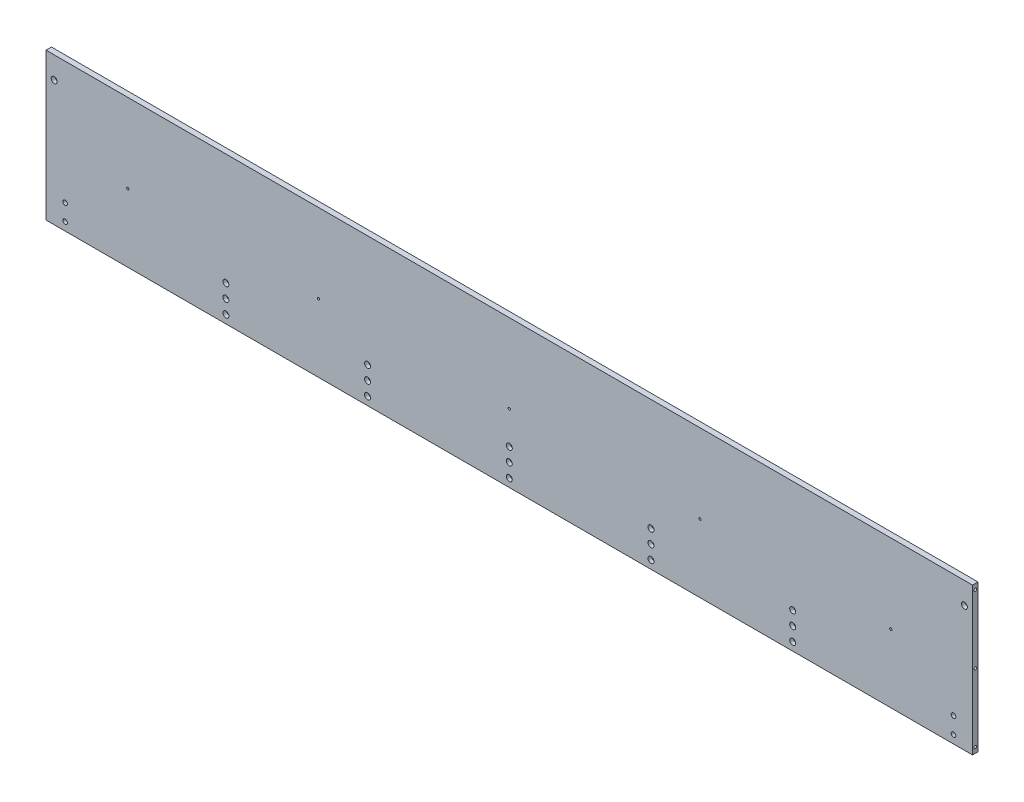
SolidWorks part; units mm, degrees
material "A3钢"
ref_plane "前视基准面" through (0, 0, 0) normal (0, 0, 1) x (1, 0, 0)
ref_plane "上视基准面" through (0, 0, 0) normal (0, 1, 0) x (1, 0, 0)
ref_plane "右视基准面" through (0, 0, 0) normal (1, 0, 0) x (0, 0, -1)
sketch "草图1" plane through (0, 0, 0) normal (0, 0, 1) x (1, 0, 0)
  line L1 (-850, -135) -> (850, -135)
  line L2 (-850, -135) -> (-850, 135)
  line L3 (-850, 135) -> (850, 135)
  line L4 (850, -135) -> (850, 135)
  line L5 (-850, -135) -> (850, 135) construction
  line L6 (-850, 135) -> (850, -135) construction
  point P0 (0, 0)
  dimension "D1" = 1700
  dimension "D2" = 270
extrude "凸台-拉伸1" add sketch "草图1" along normal mid plane 10
sketch "草图2" plane through (0, 0, 5) normal (0, 0, 1) x (1, 0, 0)
  line L0 (0, 619.8775) -> (0, -680.849) construction
  line L1 (-850, 135) -> (-850, -135) construction
  line L2 (-842.5, -90) -> (842.5, -90)
  line L3 (-842.5, -90) -> (-842.5, 90)
  line L4 (-842.5, 90) -> (842.5, 90)
  line L5 (842.5, -90) -> (842.5, 90)
  line L6 (-842.5, -90) -> (842.5, 90) construction
  line L7 (-842.5, 90) -> (842.5, -90) construction
  line L8 (-842.5, 0) -> (1266.3795, 0) construction
  point P3 (0, 0)
  dimension "D1" = 7.5
  dimension "D2" = 180
sketch "草图3" plane through (-850, 0, 0) normal (-1, 0, 0) x (0, 0, 1)
  line L0 (-50.321, 0) -> (47.9805, 0) construction
  line L1 (0, 125) -> (0, -125) construction
  dimension "D1" = 250
hole_wizard "M6 螺纹孔1" positions "3D草图1" profile "草图5" tap size "M6" standard "GB"
sketch3d "3D草图1"
  line L1 (-850, 125, 0) -> (-850, -125, 0) construction
  point P0 (-850, 125, 0)
  point P3 (-850, -125, 0)
  point P10 (-850, 0, 0)
sketch "草图5" plane through (-850, 125, 0) normal (0, 1, 0) x (0, 0, 1)
  line L0 (0, 0) -> (0, 16.5022)
  line L1 (0, 16.5022) -> (2.5, 15)
  line L2 (2.5, 15) -> (2.5, 0)
  line L5 (2.5, 0) -> (0, 0)
  line L10 (0, 16.5022) -> (-2.5, 15) construction
  line L11 (0, -6.35) -> (0, 107.95) construction
  dimension "螺纹孔钻头直径" = 5
  dimension "螺纹孔钻头深度" = 15
  dimension "导头角度" = 118
cosmetic thread "孔螺蚊线1" parameters "D1"=12, "D2"=6
cosmetic thread "孔螺蚊线2" parameters "D1"=12, "D2"=6
cosmetic thread "孔螺蚊线3" parameters "D1"=12, "D2"=6
mirror "镜向1" about plane through (0, 0, 0) normal (1, 0, 0) of "M6 螺纹孔1"
sketch "草图6" plane through (0, 0, 5) normal (0, 0, 1) x (1, 0, 0)
  line L0 (800, 0) -> (850, 0) construction
  line L1 (850, -135) -> (850, 135) construction
  line L2 (850, 135) -> (-850, 135) construction
  dimension "D1" = 135
  dimension "D2" = 50
sketch "草图9" plane through (0, 0, -5) normal (0, 0, -1) x (-1, 0, 0)
  line L0 (-951.5279, 0) -> (876.388, 0) construction
  line L1 (-690, 47) -> (-690, -49) construction
  line L2 (-850, -135) -> (-850, 135) construction
  line L3 (0, 268.067) -> (0, -611.0479) construction
  line L4 (690, 47) -> (690, -49) construction
  dimension "D1" = 96
  dimension "D2" = 49
  dimension "D3" = 160
sketch "草图14" plane through (0, 0, 5) normal (0, 0, 1) x (1, 0, 0)
  line L0 (-850, 135) -> (-850, -135) construction
  line L1 (-850, -135) -> (850, -135) construction
  circle A0 centre (-800, -105) radius 4
  dimension "D1" = 50
  dimension "D2" = 30
  dimension "D3" = 8
sketch "草图17" plane through (0, 0, 5) normal (0, 0, 1) x (1, 0, 0)
  line L0 (0, 0) -> (0, 782.9134) construction
  line L1 (-780, -70) -> (-520, -70) construction
  line L2 (-520, -70) -> (-260, -70) construction
  line L3 (-260, -70) -> (0, -70) construction
  line L5 (-850, -135) -> (850, -135) construction
  dimension "D1" = 65
  dimension "D2" = 260
hole_wizard "打孔尺寸(%根据)内六角圆柱头螺钉的类型3" positions "3D草图6" profile "草图18" counterbore size "M6" standard "GB" end condition through all
sketch3d "3D草图6"
  point P6 (-520, -70, 5)
  point P9 (-260, -70, 5)
  point P12 (0, -70, 5)
sketch "草图18" plane through (-520, -70, 5) normal (1, 0, 0) x (0, -1, 0)
  line L0 (0, 0) -> (0, 10)
  line L1 (0, 10) -> (3.3, 10)
  line L3 (3.3, 10) -> (3.3, 6.8)
  line L4 (3.3, 6.8) -> (5.5, 6.8)
  line L5 (5.5, 6.8) -> (5.5, 0)
  line L7 (5.5, 0) -> (0, 0)
  line L11 (0, -6.35) -> (0, 107.95) construction
  dimension "通孔孔直径" = 6.6
  dimension "通孔孔深度" = 10
  dimension "柱形沉头孔直径" = 11
  dimension "柱形沉头孔深度" = 6.8
mirror "镜向4" about plane through (0, 0, 0) normal (1, 0, 0) of "打孔尺寸(%根据)内六角圆柱头螺钉的类型3"
pattern_linear "阵列(线性)1" count 3 spacing 25 along (0, -1, 0) of "打孔尺寸(%根据)内六角圆柱头螺钉的类型3", "镜向4"
sketch "草图19" plane through (0, 0, 5) normal (0, 0, 1) x (1, 0, 0)
  line L0 (0, 0) -> (0, 381.1723) construction
  line L1 (350, -10) -> (-350, -10) construction
  line L2 (-350, -10) -> (-700, -10) construction
  line L4 (350, -10) -> (700, -10) construction
  line L5 (-850, -135) -> (850, -135) construction
  point P10 (0, -10)
  dimension "D1" = 125
  dimension "D2" = 350
  dimension "D3" = 350
hole_wizard "M5 螺纹孔1" positions "3D草图7" profile "草图20" tap size "M5" standard "GB" end condition through all
sketch3d "3D草图7"
  line L0 (350, -10, 5) -> (-350, -10, 5) construction
  point P0 (-700, -10, 5)
  point P3 (-350, -10, 5)
  point P7 (700, -10, 5)
  point P10 (350, -10, 5)
  point P19 (0, -10, 5)
sketch "草图20" plane through (-700, -10, 5) normal (1, 0, 0) x (0, -1, 0)
  line L0 (0, 0) -> (0, 10)
  line L1 (0, 10) -> (2.1, 10)
  line L2 (2.1, 10) -> (2.1, 0)
  line L5 (2.1, 0) -> (0, 0)
  line L11 (0, -6.35) -> (0, 107.95) construction
  dimension "通孔螺纹孔钻头直径" = 4.2
  dimension "通孔螺纹孔钻头深度" = 10
cosmetic thread "孔螺蚊线4" parameters "D2"=5
cosmetic thread "孔螺蚊线5" parameters "D2"=5
cosmetic thread "孔螺蚊线6" parameters "D2"=5
cosmetic thread "孔螺蚊线7" parameters "D2"=5
cosmetic thread "孔螺蚊线8" parameters "D2"=5
sketch "草图21" plane through (0, 0, 5) normal (0, 0, 1) x (1, 0, 0)
  line L0 (835, 95) -> (835, 135) construction
  line L1 (850, 135) -> (-850, 135) construction
  line L2 (850, -135) -> (850, 135) construction
  dimension "D1" = 40
  dimension "D2" = 15
hole_wizard "打孔尺寸(%根据)内六角圆柱头螺钉的类型3" positions "3D草图8" profile "草图22" counterbore size "M6" standard "GB" end condition through all
sketch3d "3D草图8"
  point P0 (835, 95, 5)
sketch "草图22" plane through (835, 95, 5) normal (1, 0, 0) x (0, -1, 0)
  line L0 (0, 0) -> (0, 10)
  line L1 (0, 10) -> (3.3, 10)
  line L3 (3.3, 10) -> (3.3, 6.8)
  line L4 (3.3, 6.8) -> (5.5, 6.8)
  line L5 (5.5, 6.8) -> (5.5, 0)
  line L7 (5.5, 0) -> (0, 0)
  line L11 (0, -6.35) -> (0, 107.95) construction
  dimension "通孔孔直径" = 6.6
  dimension "通孔孔深度" = 10
  dimension "柱形沉头孔直径" = 11
  dimension "柱形沉头孔深度" = 6.8
sketch "草图23" plane through (0, 0, 5) normal (0, 0, 1) x (1, 0, 0)
  line L0 (-835, 95) -> (-835, 135) construction
  line L1 (850, 135) -> (-850, 135) construction
  line L2 (-850, 135) -> (-850, -135) construction
  dimension "D1" = 40
  dimension "D2" = 15
hole_wizard "打孔尺寸(%根据)内六角圆柱头螺钉的类型3" positions "3D草图9" profile "草图24" counterbore size "M6" standard "GB" end condition through all
sketch3d "3D草图9"
  point P0 (-835, 95, 5)
sketch "草图24" plane through (-835, 95, 5) normal (1, 0, 0) x (0, -1, 0)
  line L0 (0, 0) -> (0, 10)
  line L1 (0, 10) -> (3.3, 10)
  line L3 (3.3, 10) -> (3.3, 6.8)
  line L4 (3.3, 6.8) -> (5.5, 6.8)
  line L5 (5.5, 6.8) -> (5.5, 0)
  line L7 (5.5, 0) -> (0, 0)
  line L11 (0, -6.35) -> (0, 107.95) construction
  dimension "通孔孔直径" = 6.6
  dimension "通孔孔深度" = 10
  dimension "柱形沉头孔直径" = 11
  dimension "柱形沉头孔深度" = 6.8
sketch "草图25" plane through (0, 0, 5) normal (0, 0, 1) x (1, 0, 0)
  line L0 (-815, -90) -> (-815, -120) construction
  line L1 (-850, 135) -> (-850, -135) construction
  line L4 (-850, -135) -> (850, -135) construction
  dimension "D1" = 35
  dimension "D2" = 30
  dimension "D3" = 15
hole_wizard "M10 螺纹孔1" positions "3D草图10" profile "草图26" tap size "M10" standard "GB" end condition through all
sketch3d "3D草图10"
  point P0 (-815, -90, 5)
  point P3 (-815, -120, 5)
cosmetic thread "孔螺蚊线9" parameters "D2"=10
cosmetic thread "孔螺蚊线10" parameters "D2"=10
sketch "草图26" plane through (-815, -90, 5) normal (1, 0, 0) x (0, -1, 0)
  line L0 (0, 0) -> (0, 10)
  line L1 (0, 10) -> (4.25, 10)
  line L2 (4.25, 10) -> (4.25, 0)
  line L5 (4.25, 0) -> (0, 0)
  line L11 (0, -6.35) -> (0, 107.95) construction
  dimension "通孔螺纹孔钻头直径" = 8.5
  dimension "通孔螺纹孔钻头深度" = 10
mirror "镜向5" about plane through (0, 0, 0) normal (1, 0, 0) of "M10 螺纹孔1"
